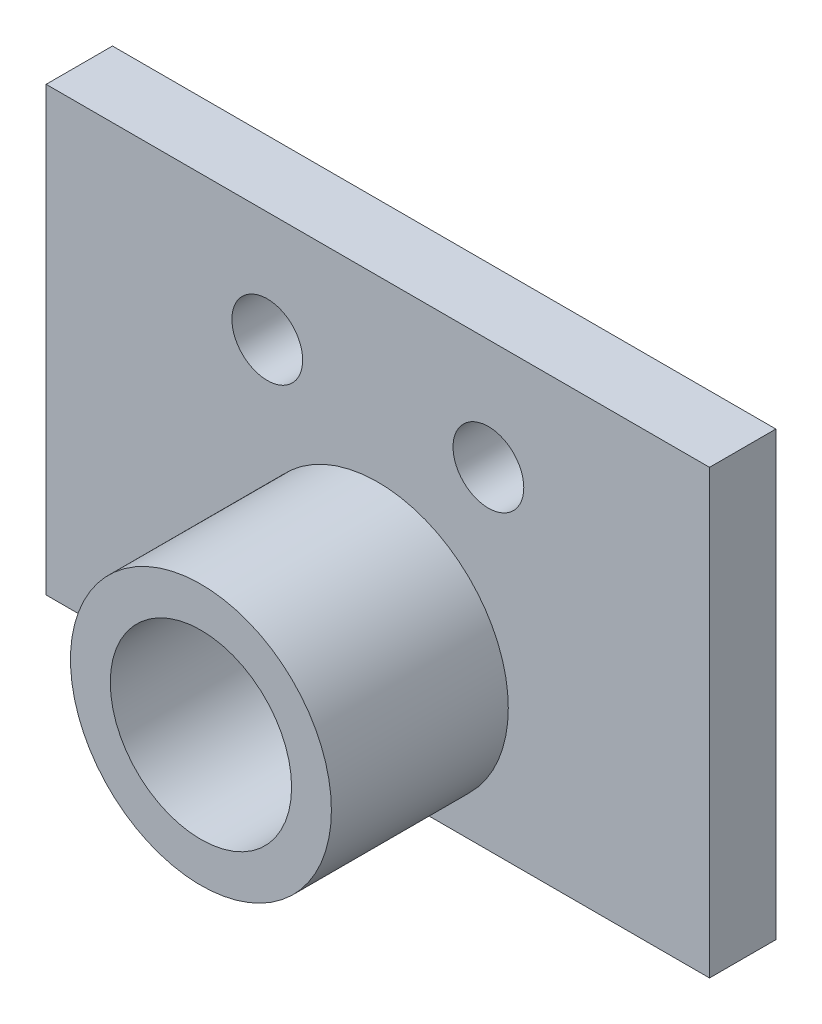
SolidWorks part; units mm, degrees
ref_plane "前视基准面" through (0, 0, 0) normal (0, 0, 1) x (1, 0, 0)
ref_plane "上视基准面" through (0, 0, 0) normal (0, 1, 0) x (1, 0, 0)
ref_plane "右视基准面" through (0, 0, 0) normal (1, 0, 0) x (0, 0, -1)
other "Configuration Table"
sketch "草图1" plane through (0, 0, 0) normal (0, 0, 1) x (1, 0, 0)
  line L0 (-3.6122, 36.0489) -> (-3.6122, 16.0489) construction
  line L1 (-18.6122, 36.0489) -> (11.3878, 36.0489)
  line L2 (-18.6122, 36.0489) -> (-18.6122, 16.0489)
  line L3 (-18.6122, 16.0489) -> (11.3878, 16.0489)
  line L4 (11.3878, 36.0489) -> (11.3878, 16.0489)
  line L5 (-3.6122, 31.0489) -> (-8.6122, 31.0489) construction
  line L6 (-8.6122, 31.0489) -> (-8.6122, 36.0489) construction
  line L7 (-3.6122, 31.0489) -> (1.3878, 31.0489) construction
  line L8 (1.3878, 31.0489) -> (1.3878, 36.0489) construction
  circle A0 centre (-8.6122, 31.0489) radius 1.6
  circle A1 centre (1.3878, 31.0489) radius 1.6
  circle A2 centre (-3.6122, 22.0732) radius 4.1
  point P15 (0, 0)
  point P16 (-3.6122, 22.0732)
  dimension "D3" = 5
  dimension "D7" = 8.2
  dimension "D8" = 3.2
  dimension "D1" = 30
  dimension "D2" = 20
  dimension "D4" = 5
  dimension "D5" = 5
  dimension "D6" = 5
extrude "凸台-拉伸1" add sketch "草图1" along normal blind 3
sketch "草图2" plane through (0, 0, 3) normal (0, 0, 1) x (1, 0, 0)
  circle A0 centre (-3.6122, 22.0732) radius 5.9
  circle A1 centre (-3.6122, 22.0732) radius 4.1
  circle A2 centre (-3.6122, 22.0732) radius 4.1 construction
  dimension "D1" = 1.8
extrude "凸台-拉伸2" add sketch "草图2" along normal blind 8 contours A0 | A1
